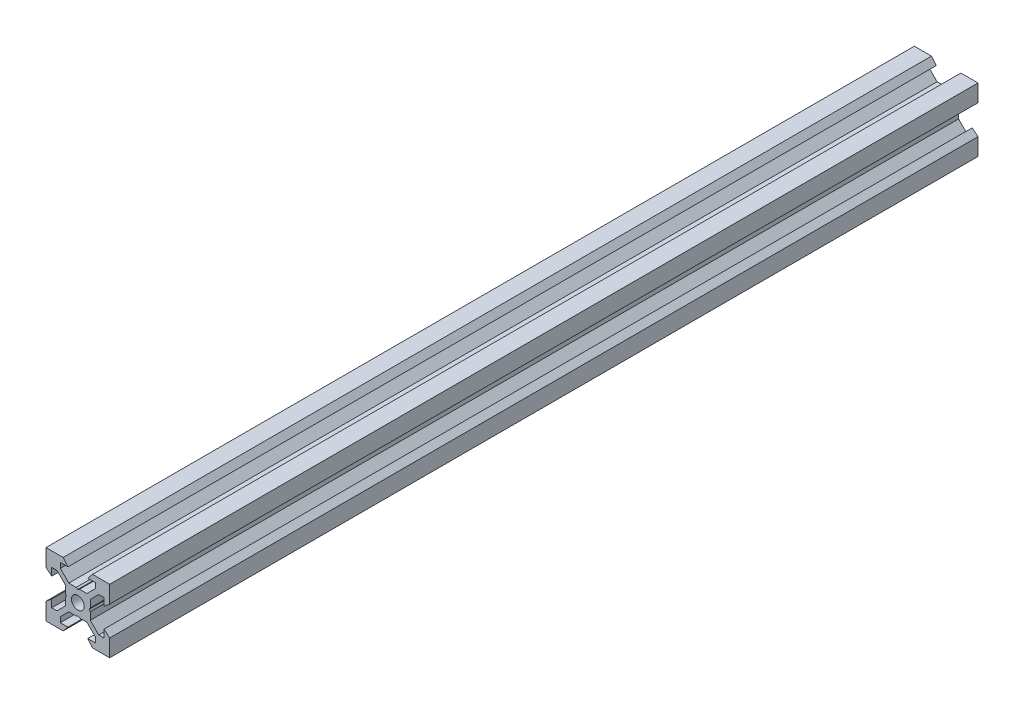
SolidWorks part; units mm, degrees
ref_plane "Front Plane" through (0, 0, 0) normal (0, 0, 1) x (1, 0, 0)
ref_plane "Top Plane" through (0, 0, 0) normal (0, 1, 0) x (1, 0, 0)
ref_plane "Right Plane" through (0, 0, 0) normal (1, 0, 0) x (0, 0, -1)
sketch "Sketch1" plane through (0, 0, 0) normal (0, 0, 1) x (1, 0, 0)
  line L0 (10, 10) -> (4.6104, 10) construction
  line L1 (10, 10) -> (10, 4.6104) construction
  line L2 (10, -10) -> (10, -4.6104) construction
  line L3 (10, -10) -> (4.6104, -10) construction
  line L4 (10, 10) -> (10, 4.6104)
  line L5 (6.5607, 5.5) -> (8.2, 5.5)
  line L6 (5.5, 8.2) -> (5.5, 6.5607)
  line L7 (10, 10) -> (4.6104, 10)
  line L8 (10, 10) -> (10, 4.6104)
  line L9 (6.5607, 5.5) -> (3.9, 2.8393)
  line L10 (5.5, 6.5607) -> (2.8393, 3.9)
  line L11 (10, 4.6104) -> (8.2, 3.1)
  line L12 (4.6104, 10) -> (3.1, 8.2)
  line L13 (8.2, 3.1) -> (8.2, 5.5)
  line L14 (3.1, 8.2) -> (5.5, 8.2)
  line L15 (-6.5607, 5.5) -> (-8.2, 5.5)
  line L16 (6.5607, -5.5) -> (8.2, -5.5)
  line L17 (3.1, -8.2) -> (5.5, -8.2)
  line L18 (8.2, -3.1) -> (8.2, -5.5)
  line L19 (4.6104, -10) -> (3.1, -8.2)
  line L20 (10, -4.6104) -> (8.2, -3.1)
  line L21 (0.5196, -3.9) -> (0, -3.6)
  line L22 (0.5196, 3.9) -> (0, 3.6)
  line L23 (3.6, 0) -> (3.9, -0.5196)
  line L24 (3.9, 0.5196) -> (3.6, 0)
  line L25 (3.9, 0.5196) -> (3.9, 2.8393)
  line L26 (2.8393, 3.9) -> (0.5196, 3.9)
  line L27 (3.9, -2.8393) -> (3.9, -0.5196)
  line L28 (2.8393, -3.9) -> (0.5196, -3.9)
  line L29 (5.5, -6.5607) -> (2.8393, -3.9)
  line L30 (6.5607, -5.5) -> (3.9, -2.8393)
  line L31 (10, -10) -> (10, -4.6104)
  line L32 (10, -10) -> (4.6104, -10)
  line L33 (5.5, -8.2) -> (5.5, -6.5607)
  line L34 (-6.5607, -5.5) -> (-8.2, -5.5)
  line L35 (10, -10) -> (10, -4.6104)
  line L36 (0, 0) -> (0, 8.2) construction
  line L37 (-10, -10) -> (-4.6104, -10) construction
  line L38 (-10, -10) -> (-10, -4.6104) construction
  line L39 (-10, 10) -> (-10, 4.6104) construction
  line L40 (-10, 10) -> (-4.6104, 10) construction
  line L41 (-10, -10) -> (-10, -4.6104)
  line L43 (-5.5, -8.2) -> (-5.5, -6.5607)
  line L44 (-10, -10) -> (-4.6104, -10)
  line L45 (-10, -10) -> (-10, -4.6104)
  line L46 (-6.5607, -5.5) -> (-3.9, -2.8393)
  line L47 (-5.5, -6.5607) -> (-2.8393, -3.9)
  line L48 (-2.8393, -3.9) -> (-0.5196, -3.9)
  line L49 (-3.9, -2.8393) -> (-3.9, -0.5196)
  line L50 (-2.8393, 3.9) -> (-0.5196, 3.9)
  line L51 (-3.9, 0.5196) -> (-3.9, 2.8393)
  line L52 (-3.9, 0.5196) -> (-3.6, 0)
  line L53 (-3.6, 0) -> (-3.9, -0.5196)
  line L54 (-0.5196, 3.9) -> (0, 3.6)
  line L55 (-0.5196, -3.9) -> (0, -3.6)
  line L56 (-10, -4.6104) -> (-8.2, -3.1)
  line L57 (-4.6104, -10) -> (-3.1, -8.2)
  line L58 (-8.2, -3.1) -> (-8.2, -5.5)
  line L59 (-3.1, -8.2) -> (-5.5, -8.2)
  line L60 (-10, -10) -> (10, -10) construction
  line L61 (-10, -10) -> (-10, 10) construction
  line L62 (-3.1, 8.2) -> (-5.5, 8.2)
  line L63 (-8.2, 3.1) -> (-8.2, 5.5)
  line L64 (-4.6104, 10) -> (-3.1, 8.2)
  line L65 (-10, 4.6104) -> (-8.2, 3.1)
  line L66 (-5.5, 6.5607) -> (-2.8393, 3.9)
  line L67 (-6.5607, 5.5) -> (-3.9, 2.8393)
  line L68 (-10, 10) -> (-10, 4.6104)
  line L69 (-10, 10) -> (-4.6104, 10)
  line L70 (-5.5, 8.2) -> (-5.5, 6.5607)
  line L71 (-10, 10) -> (10, 10) construction
  line L72 (-10, 10) -> (-10, 4.6104)
  line L73 (10, -10) -> (10, 10) construction
  line L74 (-10, -10) -> (10, 10) construction
  line L75 (-10, 10) -> (10, -10) construction
  circle A0 centre (0, 0) radius 2
  dimension "D7" = 4
  dimension "D1" = 20
  dimension "D2" = 5.3896
  dimension "D3" = 4.5
  dimension "D4" = 50
  dimension "D5" = 1.8
  dimension "D6" = 1.5104
  dimension "D8" = 5.5
  dimension "D9" = 120
  dimension "D10" = 0.3
  dimension "D11" = 2.3197
  dimension "D12" = 7.8
  dimension "D13" = 7.8
  dimension "D14" = 1.5
  dimension "D15" = 2.6607
extrude "Boss-Extrude1" add sketch "Sketch1" along normal mid plane 272.75 contours L70 L62 L64 L69 L68 L65 L63 L15 L67 L51 L52 L53 L49 L46 L34 L58 L56 L41 L44 L57 L59 L43 L47 L48 L55 L21 L28 L29 L33 L17 L19 L32 L31 L20 L18 L16 L30 L27 L23 L24 L25 L9 L5 L13 L11 L4 L7 L12 L14 L6 L10
